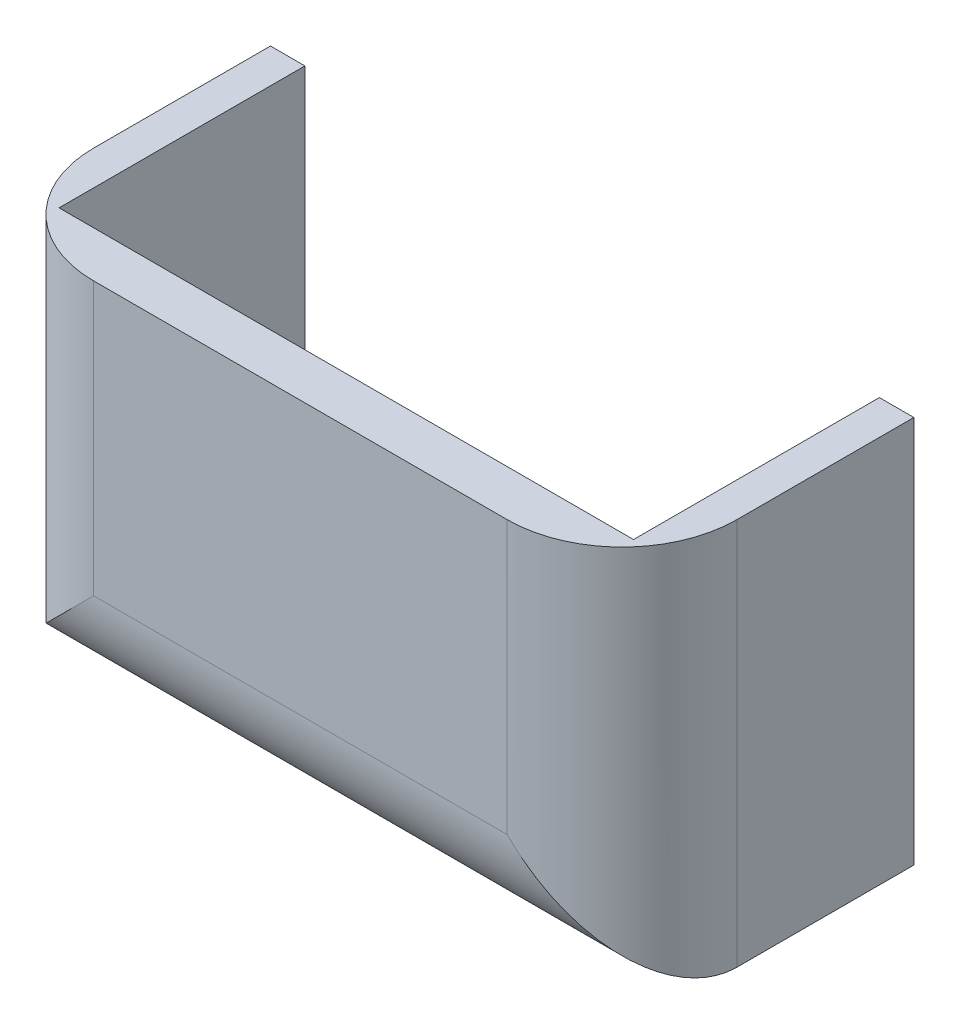
SolidWorks part; units mm, degrees
ref_plane "Front Plane" through (0, 0, 0) normal (0, 0, 1) x (1, 0, 0)
ref_plane "Top Plane" through (0, 0, 0) normal (0, 1, 0) x (1, 0, 0)
ref_plane "Right Plane" through (0, 0, 0) normal (1, 0, 0) x (0, 0, -1)
sketch "Sketch1" plane through (0, 0, 0) normal (0, 0, 1) x (1, 0, 0)
  line L1 (-28, -33.043) -> (28, -33.043)
  line L2 (-28, -33.043) -> (-28, -69.7827)
  line L3 (-28, -69.7827) -> (28, -69.7827)
  line L4 (28, -33.043) -> (28, -69.7827)
  line L6 (-25, -36.043) -> (25, -36.043)
  line L7 (-25, -36.043) -> (-25, -66.7827)
  line L8 (-25, -66.7827) -> (25, -66.7827)
  line L9 (25, -36.043) -> (25, -66.7827)
  dimension "D1" = 56
  dimension "D2" = 36.7397
  dimension "D3" = 3
  dimension "D4" = 3
  dimension "D5" = 3
  dimension "D6" = 3
extrude "Boss-Extrude1" add sketch "Sketch1" along normal blind 25.4
sketch "Sketch2" plane through (0, 0, 25.4) normal (0, 0, 1) x (1, 0, 0)
  line L1 (-28, -33.043) -> (28, -33.043)
  line L2 (-28, -33.043) -> (-28, -69.7827)
  line L3 (-28, -69.7827) -> (28, -69.7827)
  line L4 (28, -33.043) -> (28, -69.7827)
extrude "Boss-Extrude2" add sketch "Sketch2" against normal blind 4
fillet "Fillet1" radius 10 3 edges at (-28, -51.4129, 25.4) (28, -51.4129, 25.4) (0, -69.7827, 25.4)
sketch "Sketch3" plane through (0, 0, 0) normal (0, 0, -1) x (-1, 0, 0)
  line L0 (28, -33.043) -> (28, -69.7827) construction
  line L1 (-28, -33.043) -> (28, -33.043)
  line L2 (-28, -33.043) -> (-28, -36.043)
  line L3 (-28, -36.043) -> (28, -36.043)
  line L4 (28, -33.043) -> (28, -36.043)
extrude "Cut-Extrude1" cut sketch "Sketch3" against normal blind 28
